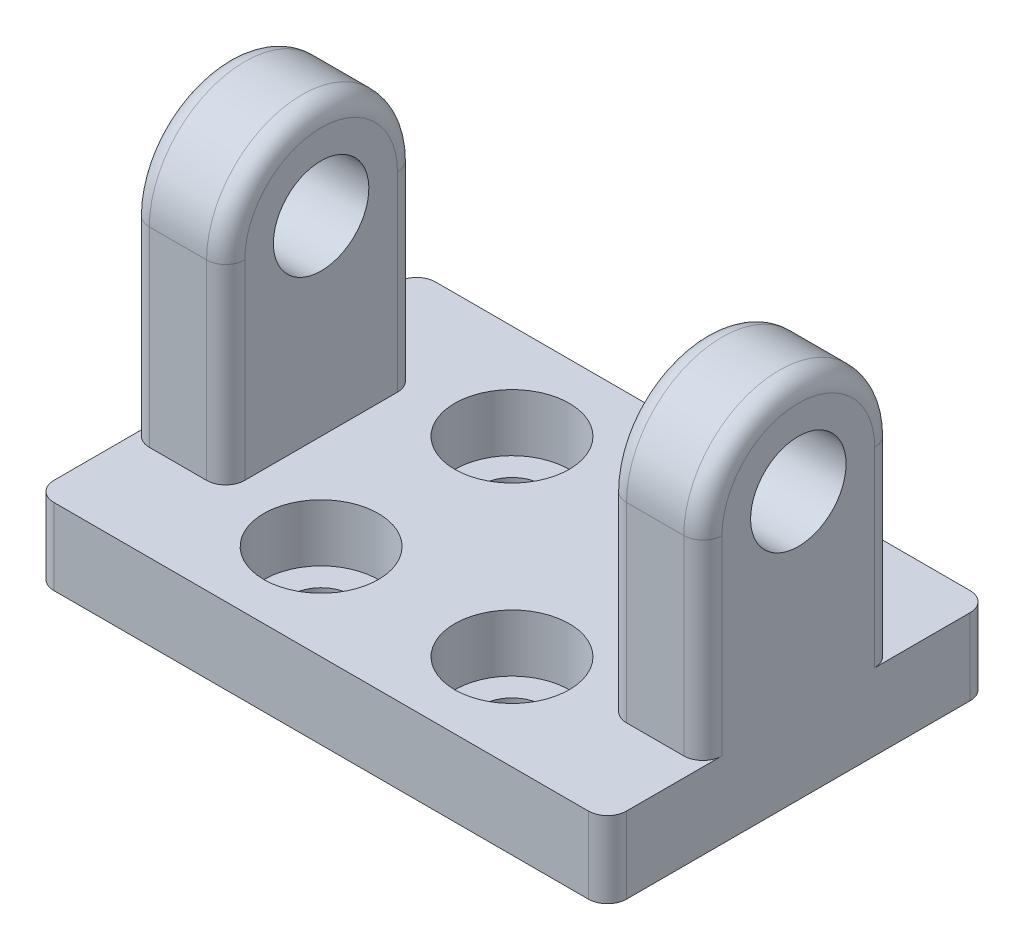
SolidWorks part; units mm, degrees
ref_plane "Plan de face" through (0, 0, 0) normal (0, 0, 1) x (1, 0, 0)
ref_plane "Plan de dessus" through (0, 0, 0) normal (0, 1, 0) x (1, 0, 0)
ref_plane "Plan de droite" through (0, 0, 0) normal (1, 0, 0) x (0, 0, -1)
sketch "Esquisse2" plane through (0, 0, 0) normal (1, 0, 0) x (0, 0, -1)
  line L0 (5, 0) -> (5, -10)
  line L2 (-5, 0) -> (-5, -10)
  line L3 (-5, -10) -> (5, -10)
  circle A0 centre (0, 0) radius 2.5
  arc A2 (5, 0) -> (-5, 0) centre (0, 0) ccw
  dimension "D1" = 5
  dimension "D2" = 10
  dimension "D3" = 5
  dimension "D4" = 5
extrude "Boss.-Extru.1" add sketch "Esquisse2" along normal mid plane 30
sketch "Esquisse4" plane through (0, -10, 0) normal (0, -1, 0) x (1, 0, 0)
  line L0 (-15, 5) -> (-15, -5) construction
  line L1 (-15, -10) -> (15, -10)
  line L2 (-15, -10) -> (-15, 10)
  line L3 (-15, 10) -> (15, 10)
  line L4 (15, -10) -> (15, 10)
  line L5 (15, 5) -> (15, -5) construction
  dimension "D1" = 20
  dimension "D4" = 10
extrude "Boss.-Extru.2" add sketch "Esquisse4" along normal blind 4
sketch "Esquisse5" plane through (0, -10, 0) normal (0, 1, 0) x (1, 0, 0)
  circle A0 centre (5, -5) radius 1.6
  circle A1 centre (5, 5) radius 1.6
  circle A2 centre (-5, 5) radius 1.6
  circle A3 centre (-5, -5) radius 1.6
  point P15 (0, 0)
  dimension "D1" = 3.2
  dimension "D2" = 10
  dimension "D3" = 10
  dimension "D4" = 5
  dimension "D5" = 5
extrude "Enlèv. mat.-Extru.1" cut sketch "Esquisse5" against normal up to next contours A0
sketch "Esquisse6" plane through (0, 0, 5) normal (0, 0, 1) x (1, 0, 0)
  line L0 (15, -10) -> (6.6, -10) construction
  line L1 (-10, 11.5437) -> (10, 11.5437)
  line L2 (-10, 11.5437) -> (-10, -10)
  line L3 (-10, -10) -> (10, -10)
  line L4 (10, 11.5437) -> (10, -10)
  line L5 (15, 0) -> (-15, 0) construction
  point P7 (0, 11.5437)
  point P11 (0, 0)
  dimension "D2" = 20
extrude "Enlèv. mat.-Extru.2" cut sketch "Esquisse6" against normal through all
sketch "Esquisse7" plane through (0, -10, 0) normal (0, 1, 0) x (1, 0, 0)
  circle A4 centre (-5, 5) radius 3
  circle A5 centre (5, 5) radius 3
  circle A6 centre (5, -5) radius 3
  circle A7 centre (-5, -5) radius 3
  dimension "D1" = 6
extrude "Enlèv. mat.-Extru.3" cut sketch "Esquisse7" against normal blind 3
fillet "Congé1" radius 1 16 edges at (10, -5, -5) (10, -5, 5) (-10, -5, 5) (-10, -5, -5) (15, -5, -5) (15, -5, 5) (-15, -5, -5) (-15, -5, 5) (10, 5, 0) (-10, 5, 0) (15, 5, 0) (-15, 5, 0) (-15, -12, -10) (-15, -12, 10) (15, -12, -10) (15, -12, 10)
